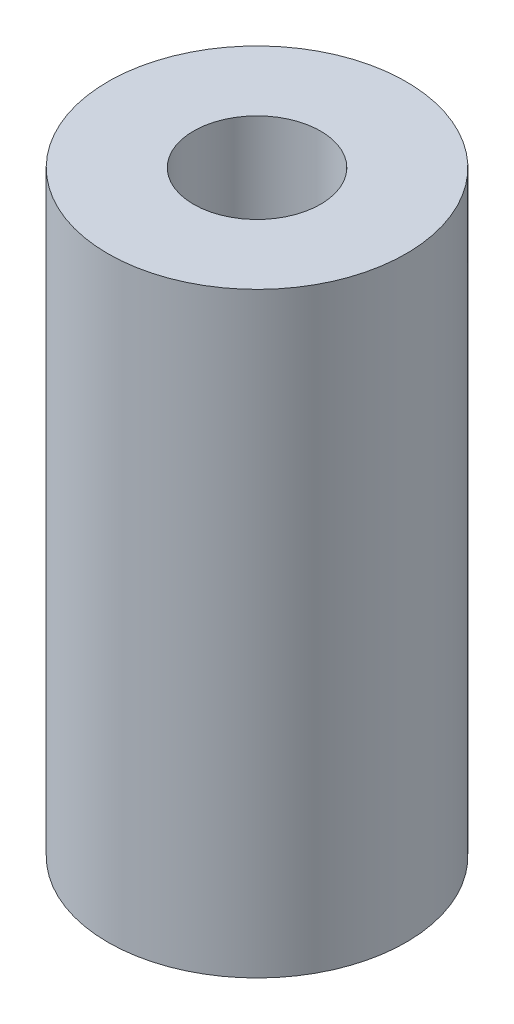
SolidWorks part; units mm, degrees
ref_plane "Front Plane" through (0, 0, 0) normal (0, 0, 1) x (1, 0, 0)
ref_plane "Top Plane" through (0, 0, 0) normal (0, 1, 0) x (1, 0, 0)
ref_plane "Right Plane" through (0, 0, 0) normal (1, 0, 0) x (0, 0, -1)
sketch "Sketch1" plane through (0, 0, 0) normal (0, 1, 0) x (1, 0, 0)
  circle A0 centre (0, 0) radius 3.175
  dimension "D1" = 6.35
extrude "Boss-Extrude1" add sketch "Sketch1" along normal blind 12.7
hole_wizard "Tap Drill for #6-32 Tap1" positions "Sketch3" profile "Sketch2" hole size "#6-32" standard "ANSI Inch" end condition through all
sketch "Sketch3" plane through (0, 12.7, 0) normal (0, 1, 0) x (1, 0, 0)
  point P0 (0, 0)
sketch "Sketch2" plane through (0, 12.7, 0) normal (1, 0, 0) x (0, 0, 1)
  line L0 (0, 0) -> (0, 12.7)
  line L1 (0, 12.7) -> (1.3525, 12.7)
  line L2 (1.3525, 12.7) -> (1.3525, 0)
  line L5 (1.3525, 0) -> (0, 0)
  line L11 (0, -6.35) -> (0, 107.95) construction
  dimension "Thru Hole Dia." = 2.7051
  dimension "Thru Hole Depth" = 12.7
